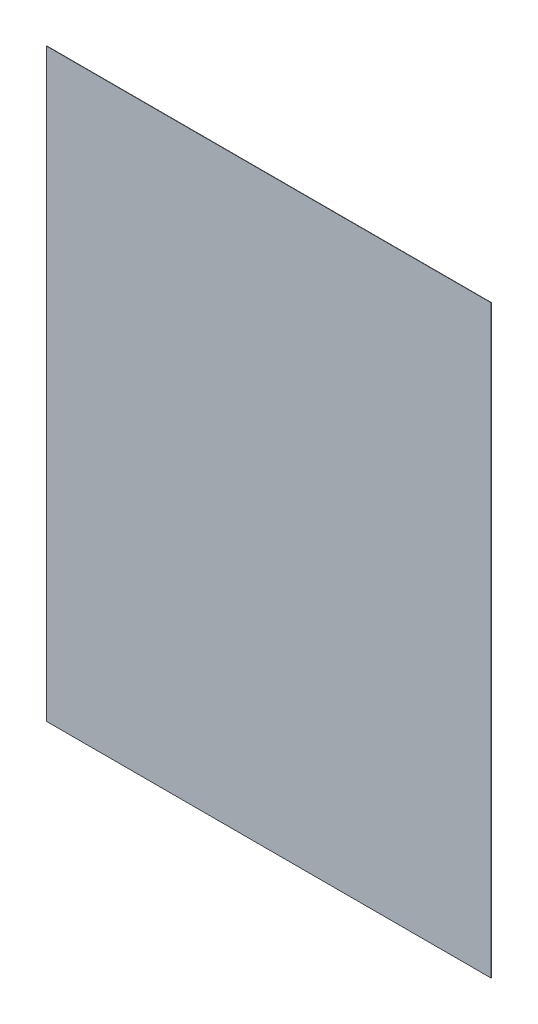
SolidWorks part; units mm, degrees
material "A123 Amp20 Aluminum Laminate"
ref_plane "Front Plane" through (0, 0, 0) normal (0, 0, 1) x (1, 0, 0)
ref_plane "Top Plane" through (0, 0, 0) normal (0, 1, 0) x (1, 0, 0)
ref_plane "Right Plane" through (0, 0, 0) normal (1, 0, 0) x (0, 0, -1)
sketch "Sketch1" plane through (0, 0, 0) normal (0, 0, 1) x (1, 0, 0)
  line L1 (-78.05, 102.75) -> (78.05, 102.75)
  line L2 (-78.05, 102.75) -> (-78.05, -102.75)
  line L3 (-78.05, -102.75) -> (78.05, -102.75)
  line L4 (78.05, 102.75) -> (78.05, -102.75)
  line L5 (-78.05, 102.75) -> (78.05, -102.75) construction
  line L6 (-78.05, -102.75) -> (78.05, 102.75) construction
  point P0 (0, 0)
  dimension "D1" = 156.1
  dimension "D2" = 205.5
extrude "Pouch" add sketch "Sketch1" along normal blind 0.112
